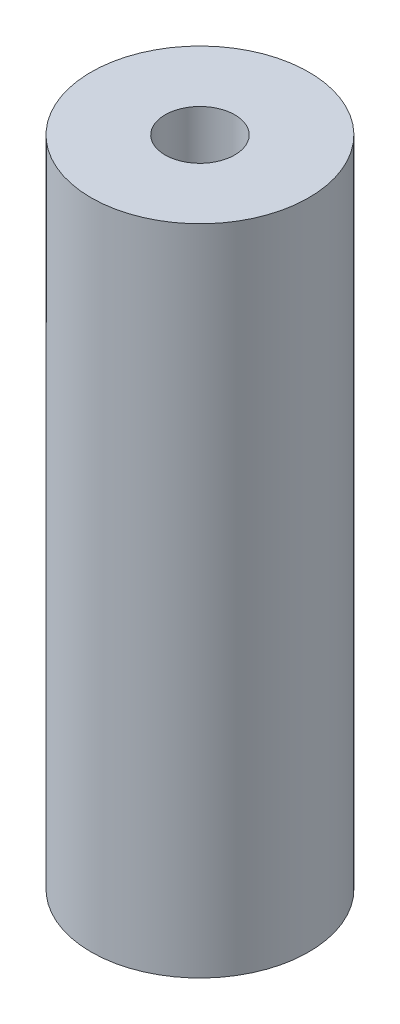
SolidWorks part; units mm, degrees
ref_plane "Front Plane" through (0, 0, 0) normal (0, 0, 1) x (1, 0, 0)
ref_plane "Top Plane" through (0, 0, 0) normal (0, 1, 0) x (1, 0, 0)
ref_plane "Right Plane" through (0, 0, 0) normal (1, 0, 0) x (0, 0, -1)
sketch "Sketch1" plane through (0, 0, 0) normal (0, 1, 0) x (1, 0, 0)
  circle A0 centre (0, 0) radius 4.064
  circle A1 centre (0, 0) radius 12.7
  dimension "D1" = 8.128
  dimension "D2" = 25.4
extrude "Boss-Extrude1" add sketch "Sketch1" along normal blind 76.2
